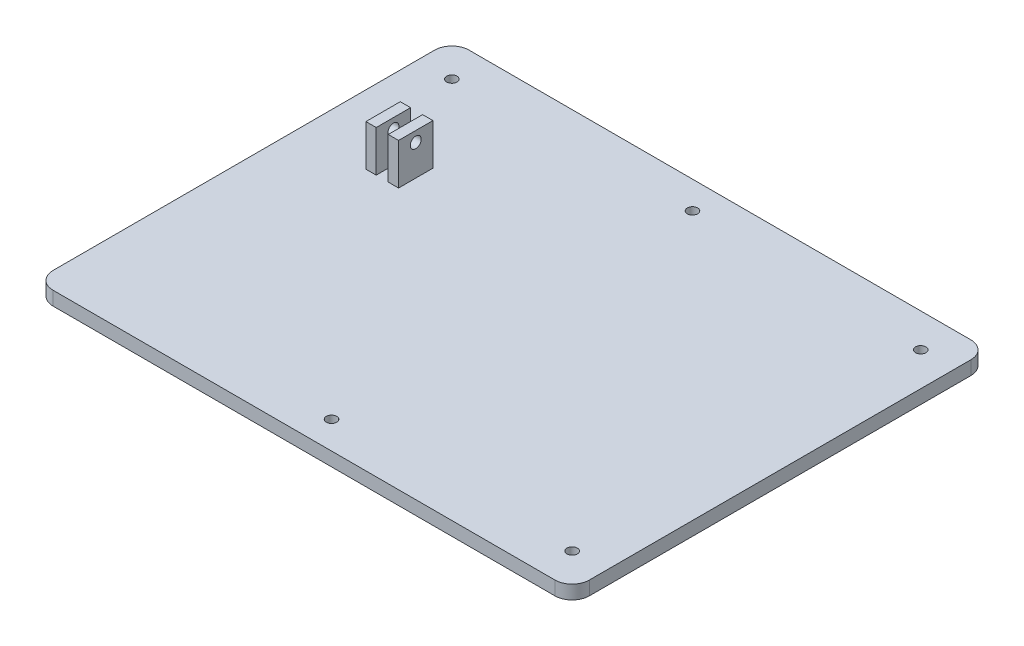
SolidWorks part; units mm, degrees
ref_plane "Front Plane" through (0, 0, 0) normal (0, 0, 1) x (1, 0, 0)
ref_plane "Top Plane" through (0, 0, 0) normal (0, 1, 0) x (1, 0, 0)
ref_plane "Right Plane" through (0, 0, 0) normal (1, 0, 0) x (0, 0, -1)
sketch "Sketch1" plane through (0, 0, 0) normal (0, 1, 0) x (1, 0, 0)
  line L1 (-124.3473, -95.7811) -> (124.3473, -95.7811)
  line L2 (-124.3473, -95.7811) -> (-124.3473, 95.7811)
  line L3 (-124.3473, 95.7811) -> (124.3473, 95.7811)
  line L4 (124.3473, -95.7811) -> (124.3473, 95.7811)
  line L5 (-124.3473, -95.7811) -> (124.3473, 95.7811) construction
  line L6 (-124.3473, 95.7811) -> (124.3473, -95.7811) construction
  point P0 (0, 0)
extrude "Boss-Extrude1" add sketch "Sketch1" along normal blind 4
sketch "Sketch2" plane through (0, 4, 0) normal (0, 1, 0) x (1, 0, 0)
  line L1 (-53.628, 20.2189) -> (-53.628, -90.7811) construction
  line L2 (97.372, 25.2189) -> (-48.628, 25.2189) construction
  line L3 (102.372, -90.7811) -> (102.372, 20.2189) construction
  line L5 (-53.628, 20.2189) -> (-53.628, -90.7811)
  line L6 (97.372, 25.2189) -> (-48.628, 25.2189)
  line L7 (102.372, -90.7811) -> (102.372, 20.2189)
  line L8 (124.3473, -95.7811) -> (124.3473, 95.7811) construction
  line L9 (124.3473, 95.7811) -> (-124.3473, 95.7811) construction
  line L10 (-124.3473, 95.7811) -> (-124.3473, -95.7811) construction
  line L11 (124.3473, -95.7811) -> (124.3473, 95.7811)
  line L12 (124.3473, 95.7811) -> (-124.3473, 95.7811)
  line L13 (-124.3473, 95.7811) -> (-124.3473, -95.7811)
  line L14 (-48.628, -95.7811) -> (-124.3473, -95.7811)
  line L15 (97.372, -95.7811) -> (124.3473, -95.7811)
  arc A0 (-53.628, -90.7811) -> (-48.628, -95.7811) centre (-48.628, -90.7811) ccw construction
  arc A1 (-48.628, 25.2189) -> (-53.628, 20.2189) centre (-48.628, 20.2189) ccw construction
  arc A2 (102.372, 20.2189) -> (97.372, 25.2189) centre (97.372, 20.2189) ccw construction
  arc A3 (97.372, -95.7811) -> (102.372, -90.7811) centre (97.372, -90.7811) ccw construction
  arc A4 (-53.628, -90.7811) -> (-48.628, -95.7811) centre (-48.628, -90.7811) ccw
  arc A5 (-48.628, 25.2189) -> (-53.628, 20.2189) centre (-48.628, 20.2189) ccw
  arc A6 (102.372, 20.2189) -> (97.372, 25.2189) centre (97.372, 20.2189) ccw
  arc A7 (97.372, -95.7811) -> (102.372, -90.7811) centre (97.372, -90.7811) ccw
extrude "Cut-Extrude1" cut sketch "Sketch2" against normal blind 10
sketch "Sketch3" plane through (0, 4, 0) normal (0, 1, 0) x (1, 0, 0)
  line L0 (96.372, 19.2189) -> (88.7654, 11.6123) construction
  line L1 (91.6353, 16.349) -> (94.2917, 13.6926) construction
  line L2 (96.372, -89.7811) -> (88.7654, -82.1745) construction
  line L3 (92.5687, -85.9778) -> (95.9213, -82.6251) construction
  line L4 (-47.628, 19.2189) -> (-40.0214, 11.6123) construction
  line L5 (-42.0348, 17.2055) -> (-45.925, 13.3153) construction
  line L6 (14.372, 22.2189) -> (34.372, 22.2189) construction
  line L7 (24.372, 22.2189) -> (24.372, 12.2189) construction
  line L8 (29.5065, 17.2189) -> (19.7601, 17.2189) construction
  line L9 (34.372, -92.7811) -> (14.372, -92.7811) construction
  line L10 (24.372, -92.7811) -> (24.372, -82.7811) construction
  line L11 (29.5065, -87.7811) -> (18.0193, -87.7811) construction
  circle A0 centre (-43.8247, 15.4156) radius 1.5
  circle A1 centre (24.372, 17.2189) radius 1.5
  circle A2 centre (92.5687, 15.4156) radius 1.5
  circle A3 centre (24.372, -87.7811) radius 1.5
  circle A4 centre (92.5687, -85.9778) radius 1.5
  dimension "D1" = 3
  dimension "D2" = 3
  dimension "D3" = 3
  dimension "D4" = 3
  dimension "D5" = 3
extrude "Cut-Extrude2" cut sketch "Sketch3" against normal blind 4
sketch "Sketch10" plane through (0, 4, 0) normal (0, 1, 0) x (1, 0, 0)
  line L0 (-53.628, -90.7811) -> (-53.628, 20.2189) construction
  line L1 (-30.628, -9.7811) -> (-33.628, -9.7811)
  line L2 (-30.628, -9.7811) -> (-30.628, -19.7811)
  line L3 (-30.628, -19.7811) -> (-33.628, -19.7811)
  line L4 (-33.628, -9.7811) -> (-33.628, -19.7811)
  line L5 (-48.628, 25.2189) -> (97.372, 25.2189) construction
  line L7 (-24.128, -9.7811) -> (-27.128, -9.7811)
  line L8 (-24.128, -9.7811) -> (-24.128, -19.7811)
  line L9 (-24.128, -19.7811) -> (-27.128, -19.7811)
  line L10 (-27.128, -9.7811) -> (-27.128, -19.7811)
  dimension "D1" = 20
  dimension "D2" = 3
  dimension "D3" = 35
  dimension "D4" = 10
  dimension "D5" = 3.5
  dimension "D6" = 3
extrude "Boss-Extrude2" add sketch "Sketch10" along normal blind 12
ref_plane "Plane1" through (-33.628, 0, 0) normal (-1, 0, 0) x (0, 0, 1)
sketch "Sketch12" plane through (-33.628, 0, 0) normal (-1, 0, 0) x (0, 0, 1)
  line L0 (14.7811, 16) -> (14.7811, -2.4339) construction
  line L1 (9.7811, 16) -> (19.7811, 16) construction
  circle A0 centre (14.7811, 13) radius 1.6
  dimension "D1" = 3.2
  dimension "D2" = 3
extrude "Cut-Extrude3" cut sketch "Sketch12" against normal blind 10
ref_plane "Plane2" through (0, 4, 0) normal (0, 1, 0) x (1, 0, 0)
sketch "Sketch13" plane through (0, 4, 0) normal (0, 1, 0) x (1, 0, 0)
  circle A0 centre (-29.1272, -15.0292) radius 1
  dimension "D1" = 2
extrude "Cut-Extrude4" cut sketch "Sketch13" against normal blind 6
